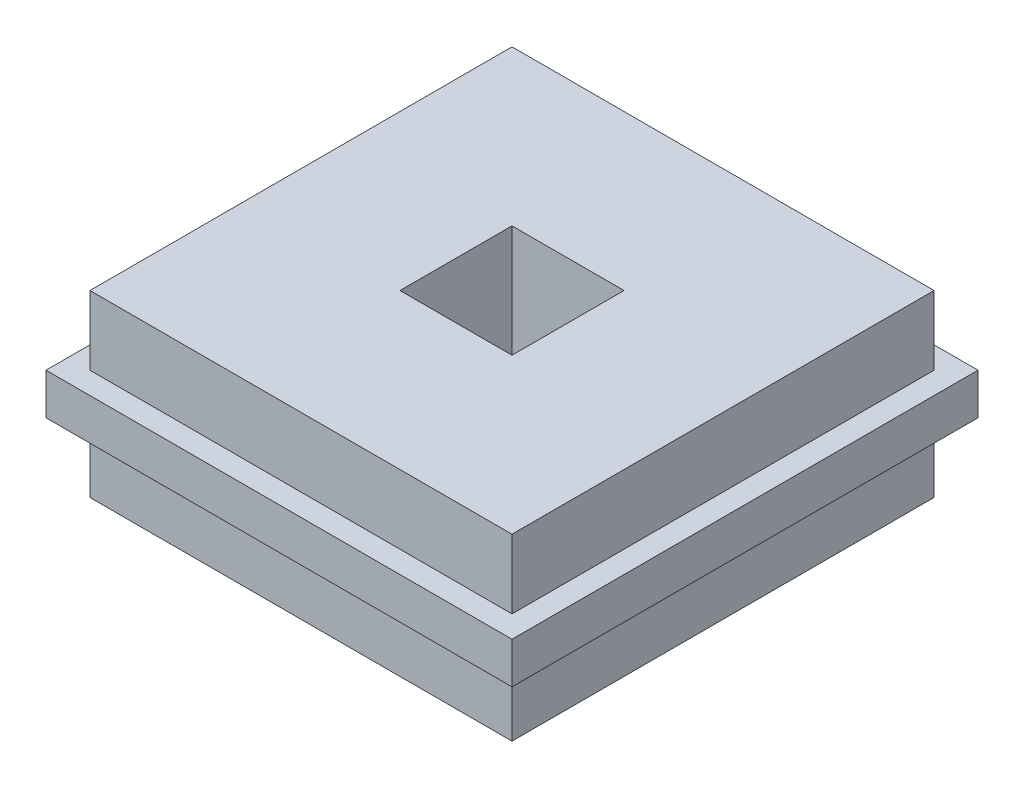
SolidWorks part; units mm, degrees
ref_plane "Front" through (0, 0, 0) normal (0, 0, 1) x (1, 0, 0)
ref_plane "Top" through (0, 0, 0) normal (0, 1, 0) x (1, 0, 0)
ref_plane "Right" through (0, 0, 0) normal (1, 0, 0) x (0, 0, -1)
sketch "Sketch1" plane through (0, 0, 0) normal (0, 1, 0) x (1, 0, 0)
  line L1 (-14.9542, 14.9542) -> (14.9542, 14.9542)
  line L2 (-14.9542, 14.9542) -> (-14.9542, -14.9542)
  line L3 (-14.9542, -14.9542) -> (14.9543, -14.9542)
  line L4 (14.9542, 14.9542) -> (14.9543, -14.9542)
  line L5 (-14.9542, 14.9542) -> (14.9543, -14.9542) construction
  line L6 (-14.9542, -14.9542) -> (14.9542, 14.9542) construction
  point P0 (0, 0)
  dimension "D1" = 29.9085
extrude "Boss-Extrude1" add sketch "Sketch1" along normal mid plane 12.7
sketch "Sketch2" plane through (0, 0, 0) normal (0, 1, 0) x (1, 0, 0)
  line L1 (16.51, -16.51) -> (-16.51, -16.51)
  line L2 (16.51, -16.51) -> (16.51, 16.51)
  line L3 (16.51, 16.51) -> (-16.51, 16.51)
  line L4 (-16.51, -16.51) -> (-16.51, 16.51)
  line L5 (16.51, -16.51) -> (-16.51, 16.51) construction
  line L6 (16.51, 16.51) -> (-16.51, -16.51) construction
  point P0 (0, 0)
  dimension "D1" = 33.02
extrude "Boss-Extrude2" add sketch "Sketch2" along normal mid plane 2.921
sketch "Sketch4" plane through (0, 6.35, 0) normal (0, 1, 0) x (1, 0, 0)
  line L1 (-3.9688, 3.9688) -> (3.9688, 3.9688)
  line L2 (-3.9688, 3.9688) -> (-3.9687, -3.9688)
  line L3 (-3.9687, -3.9688) -> (3.9688, -3.9688)
  line L4 (3.9688, 3.9688) -> (3.9688, -3.9688)
  line L5 (-3.9688, 3.9688) -> (3.9688, -3.9688) construction
  line L6 (-3.9687, -3.9688) -> (3.9688, 3.9688) construction
  point P0 (0, 0)
  dimension "D1" = 7.9375
extrude "Cut-Extrude2" cut sketch "Sketch4" against normal through all
